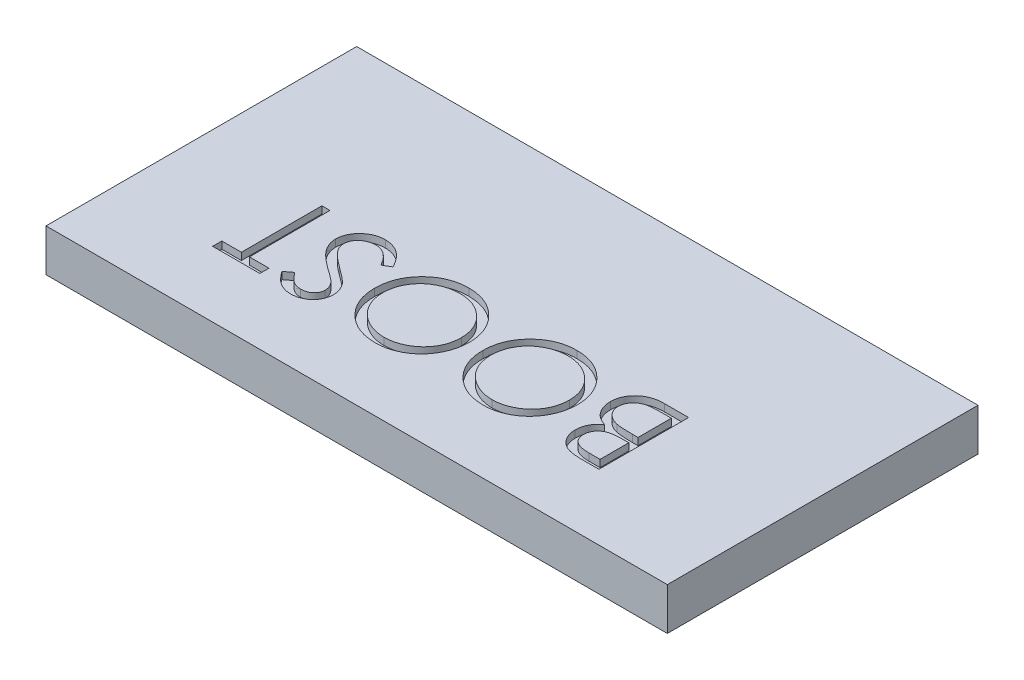
SolidWorks part; units mm, degrees
ref_plane "Front Plane" through (0, 0, 0) normal (0, 0, 1) x (1, 0, 0)
ref_plane "Top Plane" through (0, 0, 0) normal (0, 1, 0) x (1, 0, 0)
ref_plane "Right Plane" through (0, 0, 0) normal (1, 0, 0) x (0, 0, -1)
sketch "Sketch1" plane through (0, 0, 0) normal (0, 1, 0) x (1, 0, 0)
  line L1 (-11, 5.5) -> (11, 5.5)
  line L2 (-11, 5.5) -> (-11, -5.5)
  line L3 (-11, -5.5) -> (11, -5.5)
  line L4 (11, 5.5) -> (11, -5.5)
  line L5 (-11, 5.5) -> (11, -5.5) construction
  line L6 (-11, -5.5) -> (11, 5.5) construction
  point P0 (0, 0)
  dimension "D1" = 22
  dimension "D2" = 11
extrude "Boss-Extrude1" add sketch "Sketch1" along normal blind 1.4986
sketch "Sketch2" plane through (0, 1.4986, 0) normal (0, 1, 0) x (1, 0, 0)
  line L0 (6.66, 0) -> (-6.66, 0) construction
  text T0 "BOOST"
  point P4 (0, 0)
extrude "Cut-Extrude1" cut sketch "Sketch2" against normal blind 0.254
